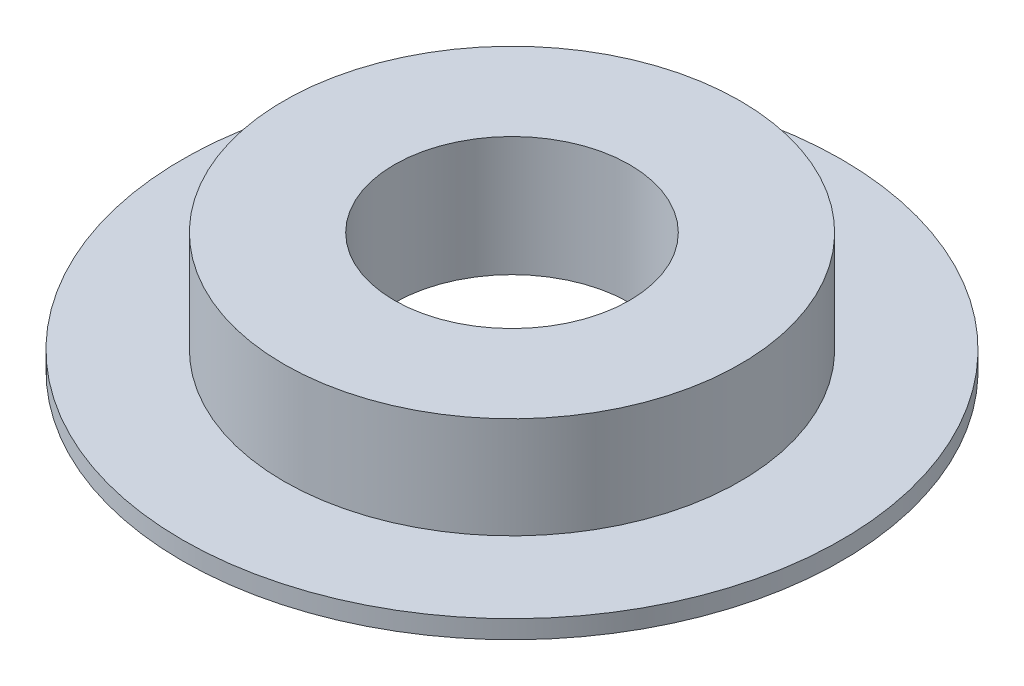
SolidWorks part; units mm, degrees
ref_plane "Alzado" through (0, 0, 0) normal (0, 0, 1) x (1, 0, 0)
ref_plane "Planta" through (0, 0, 0) normal (0, 1, 0) x (1, 0, 0)
ref_plane "Vista lateral" through (0, 0, 0) normal (1, 0, 0) x (0, 0, -1)
sketch "Croquis1" plane through (0, 0, 0) normal (0, 0, 1) x (1, 0, 0)
  line L0 (-33.5216, 13.9729) -> (-33.5216, -36.0271) construction
  line L1 (-33.5216, -11.0271) -> (-45.0216, -11.0271) construction
  line L2 (-45.1216, 8.9729) -> (-45.1216, -2.8271)
  line L3 (-33.5216, 8.9729) -> (-56.0216, 8.9729) construction
  line L4 (-45.1216, 8.9729) -> (-56.0216, 8.9729)
  line L5 (-56.0216, 8.9729) -> (-56.0216, -1.0271)
  line L6 (-56.0216, -1.0271) -> (-66.0216, -1.0271)
  line L7 (-66.0216, -1.0271) -> (-66.0216, -2.8271)
  line L8 (-66.0216, -2.8271) -> (-45.1216, -2.8271)
  dimension "D1" = 22.5
  dimension "D2" = 11.5
  dimension "D3" = 1.8
  dimension "D4" = 10
  dimension "D5" = 11.6
  dimension "D6" = 10
revolve "Revolución1" add sketch "Croquis1" angle 360 about L0
